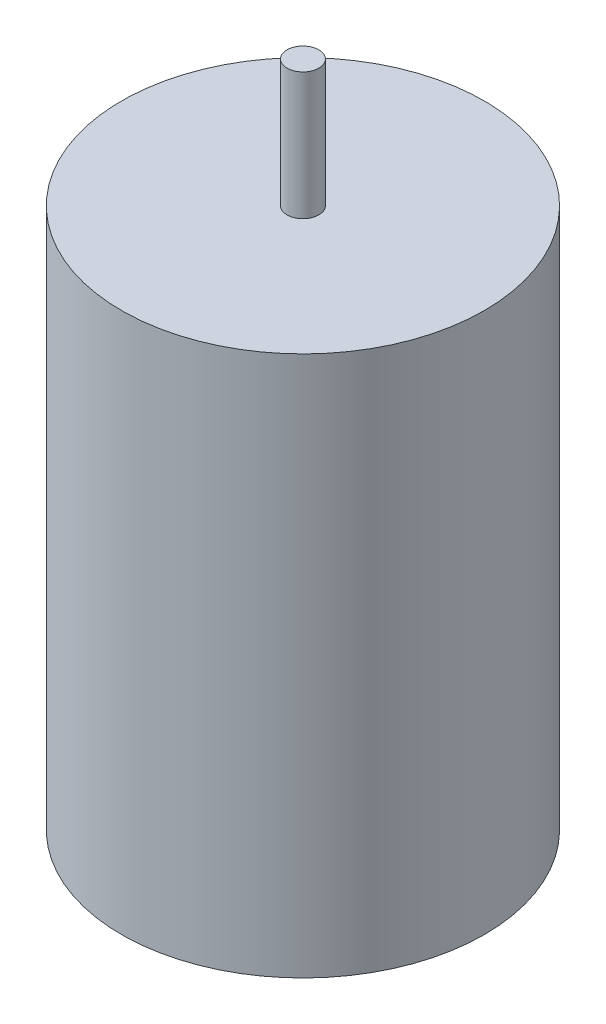
SolidWorks part; units mm, degrees
ref_plane "Front Plane" through (0, 0, 0) normal (0, 0, 1) x (1, 0, 0)
ref_plane "Top Plane" through (0, 0, 0) normal (0, 1, 0) x (1, 0, 0)
ref_plane "Right Plane" through (0, 0, 0) normal (1, 0, 0) x (0, 0, -1)
sketch "Sketch1" plane through (0, 0, 0) normal (0, 0, 1) x (1, 0, 0)
  line L0 (0, -66.7) -> (0, 66.7) construction
  line L1 (0, 66.7) -> (1.5875, 66.7)
  line L2 (1.5875, 66.7) -> (1.5875, 54)
  line L3 (1.5875, 54) -> (18.1316, 54)
  line L4 (18.1316, 54) -> (18.1316, 0)
  line L5 (18.1316, 0) -> (0, 0)
  line L6 (0, 66.7) -> (0, 0)
  point P4 (0, 0)
  dimension "D1" = 54
  dimension "D2" = 36.2632
  dimension "D3" = 3.175
  dimension "D4" = 12.7
revolve "Revolve1" add sketch "Sketch1" angle 360 about L0
